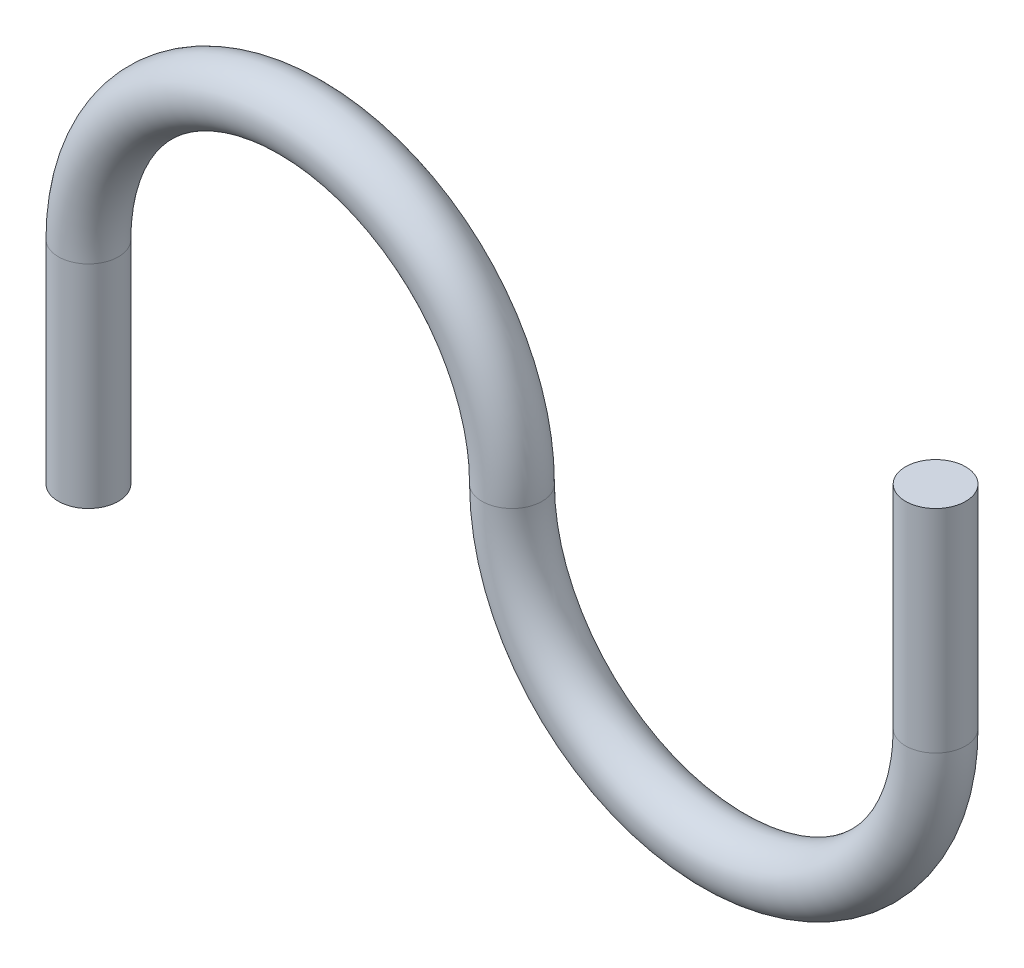
SolidWorks part; units mm, degrees
ref_plane "Plan de face" through (0, 0, 0) normal (0, 0, 1) x (1, 0, 0)
ref_plane "Plan de dessus" through (0, 0, 0) normal (0, 1, 0) x (1, 0, 0)
ref_plane "Plan de droite" through (0, 0, 0) normal (1, 0, 0) x (0, 0, -1)
sketch "Esquisse1" plane through (0, 0, 0) normal (0, 0, 1) x (1, 0, 0)
  line L0 (-22.4, 0) -> (-22.4, -22.4)
  line L1 (67.2, 0) -> (67.2, 22.4)
  arc A0 (-22.4, 0) -> (22.4, 0) centre (0, 0) cw
  arc A1 (22.4, 0) -> (67.2, 0) centre (44.8, 0) ccw
sweep "Balayage1" add path "Esquisse1" circular profile diameter 6.35 parameters "D3"=6.35
